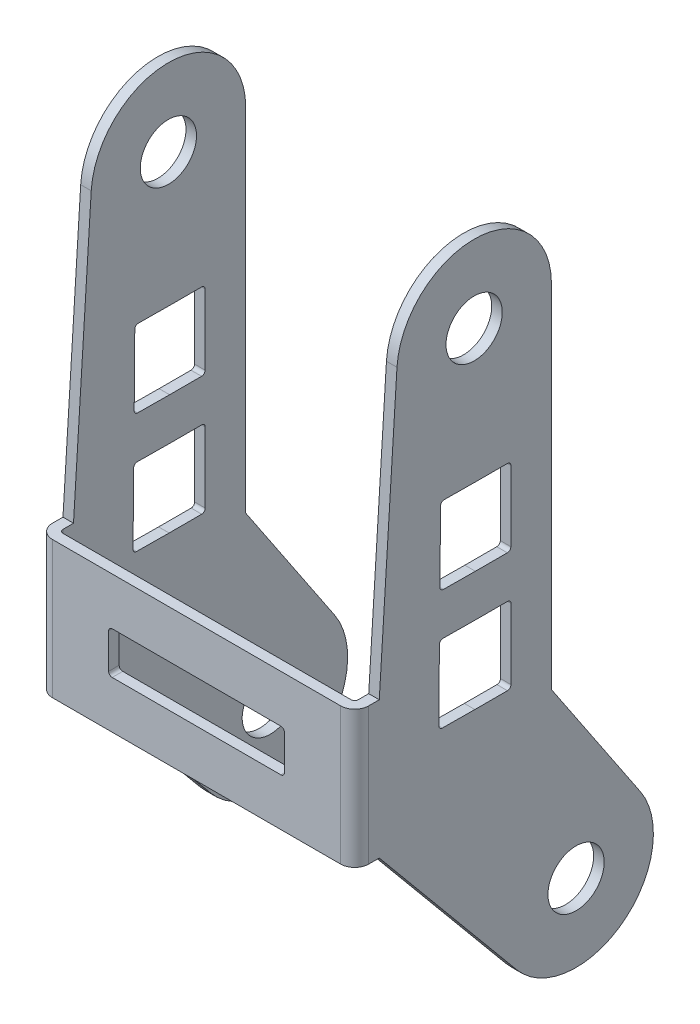
SolidWorks part; units mm, degrees
ref_plane "Front Plane" through (0, 0, 0) normal (0, 0, 1) x (1, 0, 0)
ref_plane "Top Plane" through (0, 0, 0) normal (0, 1, 0) x (1, 0, 0)
ref_plane "Right Plane" through (0, 0, 0) normal (1, 0, 0) x (0, 0, -1)
ref_plane "Plane1" through (-22.5, 0, 0) normal (-1, 0, 0) x (0, -1, 0)
sketch "Sketch1" plane through (-22.5, 0, 0) normal (-1, 0, 0) x (0, -1, 0)
  line L0 (82.0274, -6.0374) -> (58.5, 13.5)
  line L1 (58.5, 13.5) -> (39, 13.5)
  line L2 (39, 13.5) -> (-0.6975, 10.9779)
  line L3 (0, -11) -> (50, -11)
  line L4 (50, -11) -> (68.8803, -23.6405)
  arc A0 (-0.6975, 10.9779) -> (0, -11) centre (0, 0) ccw
  arc A1 (68.8803, -23.6405) -> (82.0274, -6.0374) centre (75, -14.5) ccw
extrude "Boss-Extrude1" add sketch "Sketch1" against normal blind 1.5
sketch "Sketch2" plane through (0, 0, 13.5) normal (0, 0, 1) x (1, 0, 0)
  line L0 (21, -39) -> (21, -58.5)
  line L1 (21, -58.5) -> (-22.5, -58.5)
  line L2 (-22.5, -58.5) -> (-22.5, -39)
  line L3 (-22.5, -39) -> (21, -39)
extrude "Boss-Extrude2" add sketch "Sketch2" along normal blind 3.5
sketch "Sketch3" plane through (0, 0, 13.5) normal (0, 0, -1) x (-1, 0, 0)
  line L0 (-21, -58.5) -> (21, -58.5)
  line L1 (21, -58.5) -> (21, -39)
  line L2 (21, -39) -> (-21, -39)
  line L3 (-21, -39) -> (-21, -58.5)
extrude "Cut-Extrude1" cut sketch "Sketch3" against normal blind 2
sketch "Sketch4" plane through (21, 0, 0) normal (1, 0, 0) x (0, 0, -1)
  line L0 (11, 0) -> (11, -50)
  line L1 (11, -50) -> (23.6405, -68.8803)
  line L2 (6.0374, -82.0274) -> (-13.5, -58.5)
  line L3 (-13.5, -58.5) -> (-17, -58.5)
  line L4 (-17, -58.5) -> (-17, -39)
  line L5 (-17, -39) -> (-13.5, -39)
  line L6 (-13.5, -39) -> (-10.9779, 0.6975)
  arc A0 (23.6405, -68.8803) -> (6.0374, -82.0274) centre (14.5, -75) cw
  arc A1 (-10.9779, 0.6975) -> (11, 0) centre (0, 0) cw
extrude "Boss-Extrude3" add sketch "Sketch4" along normal blind 1.5
hole_wizard "Ø8.0 (8) Diameter Hole1" positions "Sketch6" profile "Sketch5" hole size "Ø8.0" standard "ANSI Metric"
sketch "Sketch6" plane through (21, 0, 0) normal (-1, 0, 0) x (0, 0, 1)
  point P0 (-14.5, -75)
  point P1 (0, 0)
sketch "Sketch5" plane through (21, -75, -14.5) normal (0, 1, 0) x (0, 0, 1)
  line L0 (0, 0) -> (0, 1.5)
  line L1 (0, 1.5) -> (4, 1.5)
  line L2 (4, 1.5) -> (4, 0)
  line L5 (4, 0) -> (0, 0)
  line L11 (0, -6.35) -> (0, 107.95) construction
  dimension "Thru Hole Dia." = 8
  dimension "Thru Hole Depth" = 1.5
hole_wizard "Ø8.0 (8) Diameter Hole2" positions "Sketch8" profile "Sketch7" hole size "Ø8.0" standard "ANSI Metric"
sketch "Sketch8" plane through (-21, 0, 0) normal (1, 0, 0) x (0, 0, -1)
  point P0 (14.5, -75)
  point P1 (0, 0)
sketch "Sketch7" plane through (-21, -75, -14.5) normal (0, 1, 0) x (0, 0, -1)
  line L0 (0, 0) -> (0, 1.5)
  line L1 (0, 1.5) -> (4, 1.5)
  line L2 (4, 1.5) -> (4, 0)
  line L5 (4, 0) -> (0, 0)
  line L11 (0, -6.35) -> (0, 107.95) construction
  dimension "Thru Hole Dia." = 8
  dimension "Thru Hole Depth" = 1.5
fillet "Fillet1" radius 0.5 2 edges at (21, -48.75, 15.5) (-21, -48.75, 15.5)
fillet "Fillet2" radius 2 2 edges at (22.5, -48.75, 17) (-22.5, -48.75, 17)
sketch "Sketch9" plane through (0, 0, 17) normal (0, 0, 1) x (1, 0, 0)
  line L0 (0, -39) -> (0, -58.5) construction
  line L1 (20.5, -39) -> (-20.5, -39) construction
  line L2 (-20.5, -58.5) -> (20.5, -58.5) construction
  line L3 (20.5, -48.75) -> (-20.5, -48.75) construction
  line L4 (20.5, -58.5) -> (20.5, -39) construction
  line L5 (-20.5, -39) -> (-20.5, -58.5) construction
  line L6 (12.5, -45.75) -> (-12.5, -45.75)
  line L7 (-12.5, -45.75) -> (-12.5, -51.75)
  line L8 (12.5, -45.75) -> (12.5, -51.75)
  line L9 (12.5, -51.75) -> (-12.5, -51.75)
  point P17 (0, -45.75)
  point P18 (12.5, -48.75)
  point P19 (-12.5, -48.75)
  dimension "D1" = 12.5
  dimension "D2" = 3
extrude "Cut-Extrude2" cut sketch "Sketch9" against normal blind 1.5
fillet "Fillet3" radius 0.5 4 edges at (-12.5, -45.75, 16.25) (12.5, -45.75, 16.25) (12.5, -51.75, 16.25) (-12.5, -51.75, 16.25)
sketch "Sketch11" plane through (-22.5, 0, 0) normal (-1, 0, 0) x (0, 0, 1)
  line L0 (-21.0823, -83.8133) -> (-0.0668, -55.6748) construction
  line L1 (-0.0427, -61.3596) -> (-0.3489, 10.9945) construction
  line L4 (-0.1035, -47.0055) -> (5.0331, -46.9621)
  line L5 (-0.222, -19.0055) -> (-5.222, -19.0055)
  line L6 (4.94, -35.9625) -> (5.0331, -46.9621)
  line L7 (-0.1754, -30.0055) -> (-5.222, -30.0055)
  line L8 (-5.222, -19.0055) -> (-5.222, -30.0055)
  line L9 (-0.15, -36.0055) -> (-5.2402, -36.0055)
  line L10 (-0.15, -36.0055) -> (4.94, -35.9625)
  line L11 (-0.1035, -47.0055) -> (-5.2402, -47.0055)
  line L12 (-5.2402, -36.0055) -> (-5.2402, -47.0055)
  line L13 (-0.1754, -30.0055) -> (4.871, -29.9628)
  line L14 (4.7779, -18.9632) -> (4.871, -29.9628)
  line L15 (-0.222, -19.0055) -> (4.7779, -18.9632)
  arc A1 (10.9779, 0.6975) -> (-11, 0) centre (0, 0) ccw construction
  arc A2 (-23.6405, -68.8803) -> (-6.0374, -82.0274) centre (-14.5, -75) ccw construction
  dimension "D1" = 30
  dimension "D2" = 11
  dimension "D3" = 6
  dimension "D4" = 11
  dimension "D5" = 5
extrude "Cut-Extrude3" cut sketch "Sketch11" against normal blind 45
fillet "Fillet4" radius 0.5 24 edges at (-21.75, -19.0055, -0.222) (21.75, -19.0055, -0.222) (-21.75, -19.0055, -5.222) (21.75, -19.0055, -5.222) (21.75, -30.0055, -5.222) (-21.75, -30.0055, -0.1754) (21.75, -30.0055, -0.1754) (-21.75, -29.9628, 4.871) (21.75, -29.9628, 4.871) (-21.75, -18.9632, 4.7779) (21.75, -18.9632, 4.7779) (-21.75, -36.0055, -0.15) (21.75, -36.0055, -0.15) (-21.75, -36.0055, -5.2402) (21.75, -36.0055, -5.2402) (-21.75, -47.0055, -5.2402) (21.75, -47.0055, -5.2402) (-21.75, -47.0055, -0.1035) (21.75, -47.0055, -0.1035) (-21.75, -46.9621, 5.0331) (21.75, -46.9621, 5.0331) (-21.75, -35.9625, 4.94) (21.75, -35.9625, 4.94) (-21.75, -30.0055, -5.222)
